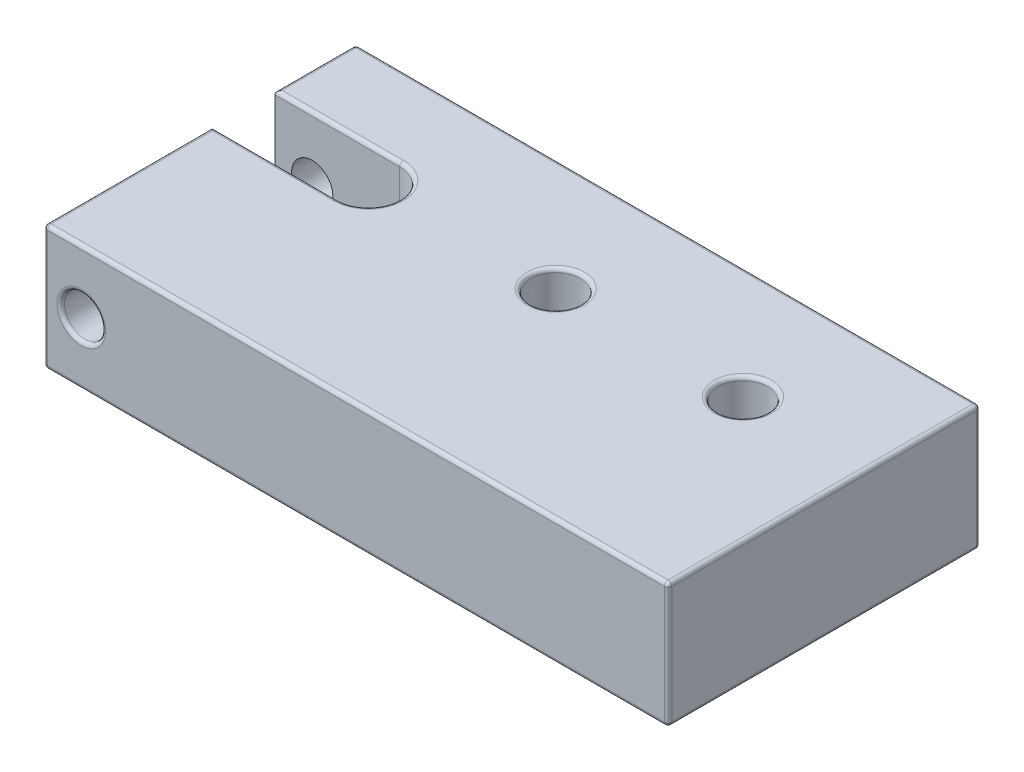
SolidWorks part; units mm, degrees
ref_plane "Front Plane" through (0, 0, 0) normal (0, 0, 1) x (1, 0, 0)
ref_plane "Top Plane" through (0, 0, 0) normal (0, 1, 0) x (1, 0, 0)
ref_plane "Right Plane" through (0, 0, 0) normal (1, 0, 0) x (0, 0, -1)
sketch "Sketch1" plane through (0, 0, 0) normal (0, 1, 0) x (1, 0, 0)
  line L0 (-10, 16) -> (10, 16) construction
  line L1 (0, 0) -> (50, 0)
  line L2 (0, 0) -> (0, 13.5)
  line L3 (0, 25) -> (50, 25)
  line L4 (50, 0) -> (50, 25)
  line L5 (0, 18.5) -> (10, 18.5)
  line L6 (0, 13.5) -> (10, 13.5)
  line L7 (0, 18.5) -> (0, 25)
  arc A1 (10, 13.5) -> (10, 18.5) centre (10, 16) ccw
  point P7 (0, 12.5)
  dimension "D1" = 50
  dimension "D2" = 25
  dimension "D3" = 5
  dimension "D4" = 9
  dimension "10" = 10
extrude "Boss-Extrude1" add sketch "Sketch1" along normal blind 10
sketch "Sketch2" plane through (0, 10, 0) normal (0, 1, 0) x (1, 0, 0)
  line L0 (58.9949, 16) -> (-7.8821, 16) construction
  line L2 (50, 0) -> (50, 25) construction
  line L3 (50, 25) -> (0, 25) construction
  circle A0 centre (40, 16) radius 2
  circle A1 centre (25, 16) radius 2
  dimension "D4" = 4
  dimension "D1" = 9
  dimension "D2" = 15
  dimension "D3" = 10
extrude "Cut-Extrude1" cut sketch "Sketch2" against normal through all
sketch "Sketch3" plane through (0, 0, 0) normal (0, 0, 1) x (1, 0, 0)
  line L0 (0, 0) -> (50, 0) construction
  line L1 (0, 10) -> (0, 0) construction
  circle A0 centre (3, 5) radius 1.65
  dimension "D1" = 3.3
  dimension "D2" = 5
  dimension "D3" = 3
extrude "Cut-Extrude2" cut sketch "Sketch3" against normal through all
fillet "Fillet1" radius 0.3 26 edges at (0, 0, -21.75) (5, 0, -18.5) (12.5, 0, -16) (5, 0, -13.5) (0, 0, -6.75) (25, 0, -14) (40, 0, -14) (5, 10, -13.5) (12.5, 10, -16) (5, 10, -18.5) (0, 10, -21.75) (0, 10, -6.75) (25, 10, -14) (40, 10, -14) (25, 10, -25) (0, 5, -25) (25, 0, -25) (50, 10, -12.5) (50, 5, -25) (50, 0, -12.5) (0, 5, 0) (25, 10, 0) (50, 5, 0) (25, 0, 0) (4.65, 5, 0) (4.65, 5, -25)
